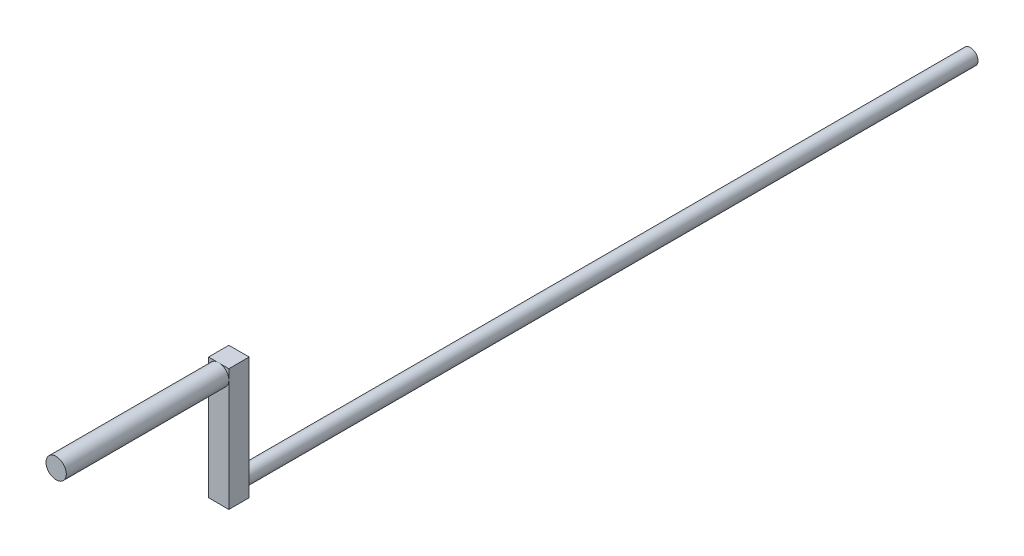
SolidWorks part; units mm, degrees
ref_plane "Front Plane" through (0, 0, 0) normal (0, 0, 1) x (1, 0, 0)
ref_plane "Top Plane" through (0, 0, 0) normal (0, 1, 0) x (1, 0, 0)
ref_plane "Right Plane" through (0, 0, 0) normal (1, 0, 0) x (0, 0, -1)
sketch "Sketch1" plane through (0, 0, 0) normal (0, 0, 1) x (1, 0, 0)
  circle A0 centre (0, 0) radius 2.3812
  dimension "D1" = 4.7625
extrude "Boss-Extrude1" add sketch "Sketch1" along normal blind 228.6
sketch "Sketch2" plane through (0, 0, 228.6) normal (0, 0, 1) x (1, 0, 0)
  line L1 (-3.134, -3.5601) -> (3.216, -3.5601)
  line L2 (-3.134, -3.5601) -> (-3.134, 34.5399)
  line L3 (-3.134, 34.5399) -> (3.216, 34.5399)
  line L4 (3.216, -3.5601) -> (3.216, 34.5399)
  dimension "D1" = 38.1
  dimension "D2" = 6.35
extrude "Boss-Extrude2" add sketch "Sketch2" along normal blind 6.35
sketch "Sketch3" plane through (0, 0, 234.95) normal (0, 0, 1) x (1, 0, 0)
  circle A0 centre (0.041, 31.4421) radius 3.175
  dimension "D1" = 6.35
extrude "Boss-Extrude3" add sketch "Sketch3" along normal blind 50.8
ref_plane "Plane1" through (2.54, 0, 0) normal (1, 0, 0) x (0, 0, -1)
